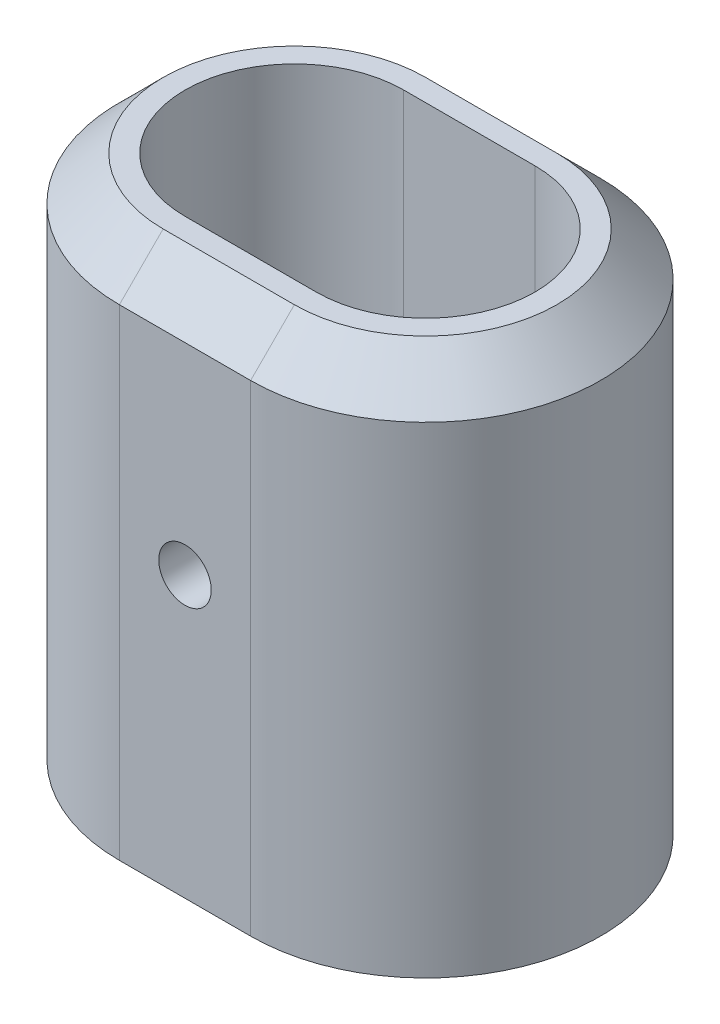
SolidWorks part; units mm, degrees
material "AISI 1020"
ref_plane "Alzado" through (0, 0, 0) normal (0, 0, 1) x (1, 0, 0)
ref_plane "Planta" through (0, 0, 0) normal (0, 1, 0) x (1, 0, 0)
ref_plane "Vista lateral" through (0, 0, 0) normal (1, 0, 0) x (0, 0, -1)
sketch "Croquis1" plane through (0, 0, 0) normal (0, 1, 0) x (1, 0, 0)
  line L0 (0, 0) -> (15, 0) construction
  line L1 (0, 12.5) -> (15, 12.5)
  line L2 (0, -12.5) -> (15, -12.5)
  line L3 (0, 0) -> (15, 0) construction
  line L4 (0, 20) -> (15, 20)
  line L5 (0, -20) -> (15, -20)
  arc A0 (0, 12.5) -> (0, -12.5) centre (0, 0) ccw
  arc A1 (15, -12.5) -> (15, 12.5) centre (15, 0) ccw
  arc A2 (0, 20) -> (0, -20) centre (0, 0) ccw
  arc A3 (15, -20) -> (15, 20) centre (15, 0) ccw
  point P3 (7.5, 0)
  point P8 (7.5, 0)
  dimension "D1" = 40
  dimension "D3" = 20
  dimension "D2" = 25
extrude "Saliente-Extruir1" add sketch "Croquis1" along normal blind 60
chamfer "Chaflán1" distance 5 angle 45 4 edges at (-20, 60, 0) (7.5, 60, 20) (7.5, 60, -20) (35, 60, 0)
sketch "Croquis2" plane through (0, 0, 20) normal (0, 0, 1) x (1, 0, 0)
  line L0 (0, 0) -> (15, 0) construction
  line L1 (0, 60) -> (15, 60) construction
  circle A0 centre (7.5, 32) radius 3
  point P4 (7.5, 0)
  dimension "D1" = 6
  dimension "D2" = 28
extrude "Cortar-Extruir1" cut sketch "Croquis2" against normal up to surface (40 mm away) up to face at (7.5, 27.5, -20)
